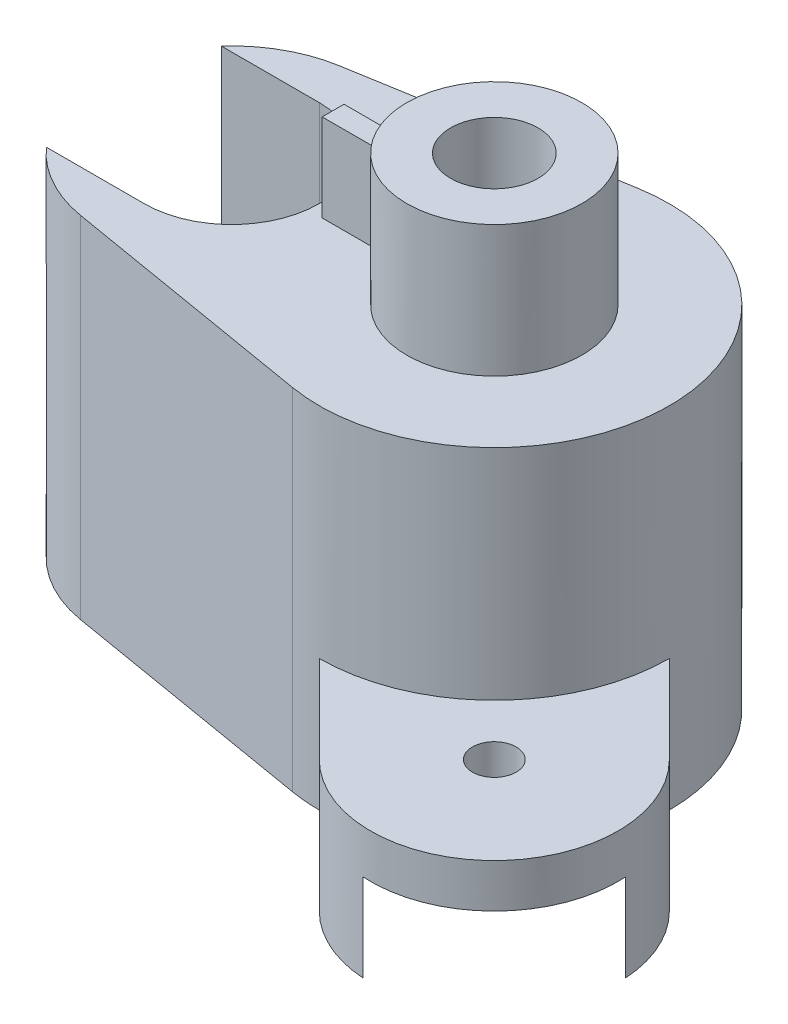
SolidWorks part; units mm, degrees
ref_plane "Front Plane" through (0, 0, 0) normal (0, 0, 1) x (1, 0, 0)
ref_plane "Top Plane" through (0, 0, 0) normal (0, 1, 0) x (1, 0, 0)
ref_plane "Right Plane" through (0, 0, 0) normal (1, 0, 0) x (0, 0, -1)
sketch "Sketch1" plane through (0, 0, 0) normal (0, 1, 0) x (1, 0, 0)
  line L0 (0, 59.2486) -> (0, -62.6796) construction
  line L1 (-6.6667, 39.4405) -> (-65, 29.5804)
  line L2 (-65, -29.5804) -> (-6.6667, -39.4405)
  arc A0 (0, -40) -> (0, 40) centre (0, 0) ccw
  arc A1 (-82.3607, 20) -> (-82.3607, -20) centre (-60, 0) ccw
  arc A2 (-82.3607, 20) -> (-65, 29.5804) centre (-60, 0) cw
  arc A3 (0, 40) -> (-6.6667, 39.4405) centre (0, 0) ccw
  arc A4 (-82.3607, -20) -> (-65, -29.5804) centre (-60, 0) ccw
  arc A5 (0, -40) -> (-6.6667, -39.4405) centre (0, 0) cw
  dimension "D1" = 80
  dimension "D3" = 30
  dimension "D2" = 60
  dimension "D4" = 20
  dimension "D5" = 20
  dimension "D6" = 20
extrude "Boss-Extrude1" add sketch "Sketch1" along normal blind 80
sketch "Sketch2" plane through (0, 0, 0) normal (0, -1, 0) x (1, 0, 0)
  circle A0 centre (0, 0) radius 30
  dimension "D1" = 60
extrude "Cut-Extrude1" cut sketch "Sketch2" against normal blind 30
sketch "Sketch3" plane through (0, 80, 0) normal (0, 1, 0) x (1, 0, 0)
  circle A0 centre (0, 0) radius 20
  dimension "D1" = 40
extrude "Boss-Extrude2" add sketch "Sketch3" along normal blind 30
sketch "Sketch4" plane through (0, 110, 0) normal (0, 1, 0) x (1, 0, 0)
  point P0 (0, 0)
hole_wizard "Ø20.0mm Dowel Hole1" positions "3DSketch1" profile "Sketch5" hole size "Ø20.0" standard "ISO"
sketch3d "3DSketch1"
  point P0 (0, 110, 0)
sketch "Sketch5" plane through (0, 110, 0) normal (1, 0, 0) x (0, 0, 1)
  line L0 (0, 0) -> (0, 36.0086)
  line L1 (0, 36.0086) -> (10, 30)
  line L2 (10, 30) -> (10, 0)
  line L5 (10, 0) -> (0, 0)
  line L10 (0, 36.0086) -> (-10, 30) construction
  line L11 (0, -6.35) -> (0, 107.95) construction
  dimension "Hole Dia." = 20
  dimension "Hole Depth" = 30
  dimension "Drill Angle" = 118
sketch "Sketch6" plane through (0, 80, 0) normal (0, 1, 0) x (1, 0, 0)
  circle A0 centre (-60, 0) radius 10
  dimension "D1" = 20
extrude "Cut-Extrude2" cut sketch "Sketch6" against normal blind 109
sketch "Sketch7" plane through (0, 80, 0) normal (0, 1, 0) x (1, 0, 0)
  line L0 (-60, 20) -> (-82.3607, 20)
  line L1 (-60, -20) -> (-82.3607, -20)
  arc A0 (-60, 20) -> (-60, -20) centre (-60, 0) cw
  arc A1 (-65, 29.5804) -> (-65, -29.5804) centre (-60, 0) ccw construction
  arc A2 (-82.3607, 20) -> (-82.3607, -20) centre (-60, 0) ccw
  circle M1 centre (-60, 0) radius 10
  arc M4 (-65, 29.5804) -> (-65, -29.5804) centre (-60, 0) ccw
  dimension "D1" = 20
  dimension "D2" = 20
  dimension "D3" = 40
  dimension "D4" = 22.3607
extrude "Cut-Extrude3" cut sketch "Sketch7" against normal blind 60 contours A0 L0 L1 M4 M1
ref_plane "Plane1" through (-6.6667, 80, 39.4405) normal (0, -1, 0) x (-1, 0, 0)
sketch "Sketch10" plane through (0, 0, 0) normal (0, -1, 0) x (1, 0, 0)
  line L0 (0, 40) -> (20, 60)
  line L1 (40, 0) -> (60, 20)
  line L2 (0, 0) -> (97.3698, 97.3698) construction
  line L3 (0, 0) -> (-141.3283, 0) construction
  line L6 (-65, -29.5804) -> (-6.6667, -39.4405)
  line L7 (-6.6667, 39.4405) -> (-65, 29.5804)
  line L8 (-65, -29.5804) -> (-6.6667, -39.4405)
  line L9 (-6.6667, 39.4405) -> (-65, 29.5804)
  arc A0 (-6.6667, -39.4405) -> (40, 0) centre (0, 0) ccw
  arc A1 (-6.6667, -39.4405) -> (-6.6667, 39.4405) centre (0, 0) ccw construction
  arc A2 (60, 20) -> (20, 60) centre (40, 40) ccw
  arc A3 (40, 0) -> (0, 40) centre (0, 0) ccw
  arc A4 (-6.6667, -39.4405) -> (-6.6667, 39.4405) centre (0, 0) ccw
  arc A5 (-65, 29.5804) -> (-65, -29.5804) centre (-60, 0) ccw
  arc A6 (0, 40) -> (-6.6667, 39.4405) centre (0, 0) ccw
  arc A7 (-65, 29.5804) -> (-65, -29.5804) centre (-60, 0) ccw
  arc M8 (-6.6667, -39.4405) -> (-6.6667, 39.4405) centre (0, 0) ccw
  dimension "D1" = 0
  dimension "D2" = 40
  dimension "D3" = 40
  dimension "D4" = 135
  dimension "D5" = 40
  dimension "D7" = 40
  dimension "D6" = 0
extrude "Boss-Extrude3" add sketch "Sketch10" against normal blind 30 contours L1 A2 L0 M8
sketch "Sketch11" plane through (0, 0, 0) normal (0, -1, 0) x (-1, 0, 0)
  line L0 (0, 0) -> (150.5849, 0) construction
  line L1 (0, 0) -> (-106.7459, -106.7459) construction
  circle A0 centre (-40, -40) radius 5
  dimension "D3" = 10
  dimension "D1" = 150.5849
  dimension "D2" = 135
extrude "Cut-Extrude4" cut sketch "Sketch11" against normal blind 30
ref_plane "Plane2" through (-6.6667, 80, 39.4405) normal (0.986, 0, 0.1667) x (0.1667, 0, -0.986)
sketch "Sketch13" plane through (0, 0, 0) normal (0, -1, 0) x (-1, 0, 0)
  line L0 (-38.2288, -68.2288) -> (0, -30)
  line L1 (-68.2288, -38.2288) -> (-30, 0)
  line L2 (0, 0) -> (119.6248, 0) construction
  line L3 (0, 0) -> (-102.2571, -102.2571) construction
  line L4 (-68.2288, -38.2288) -> (-30, 0)
  arc A0 (-60, -20) -> (-20, -60) centre (-40, -40) ccw construction
  arc A2 (-68.2288, -38.2288) -> (-38.2288, -68.2288) centre (-40, -40) ccw
  arc A3 (-30, 0) -> (0, -30) centre (0, 0) ccw
  circle M1 centre (-40, -40) radius 5
  circle M3 centre (0, 0) radius 30
  arc M7 (-60, -20) -> (-20, -60) centre (-40, -40) ccw
  dimension "D1" = 135
  dimension "D2" = 30
  dimension "D3" = 30
  dimension "D4" = 0
extrude "Cut-Extrude5" cut sketch "Sketch13" against normal blind 20 contours L1 L0 M7 M3 M1
sketch "Sketch14" plane through (0, 80, 0) normal (0, 1, 0) x (1, 0, 0)
  line L1 (-19.8431, 2.5) -> (-36.8431, 2.5)
  line L2 (-19.8431, 2.5) -> (-19.8431, -2.5)
  line L3 (-19.8431, -2.5) -> (-36.8431, -2.5)
  line L4 (-36.8431, 2.5) -> (-36.8431, -2.5)
  circle A0 centre (0, 0) radius 20 construction
  dimension "D1" = 5
  dimension "D2" = 2.5
  dimension "D3" = 17
extrude "Boss-Extrude4" add sketch "Sketch14" along normal blind 20
